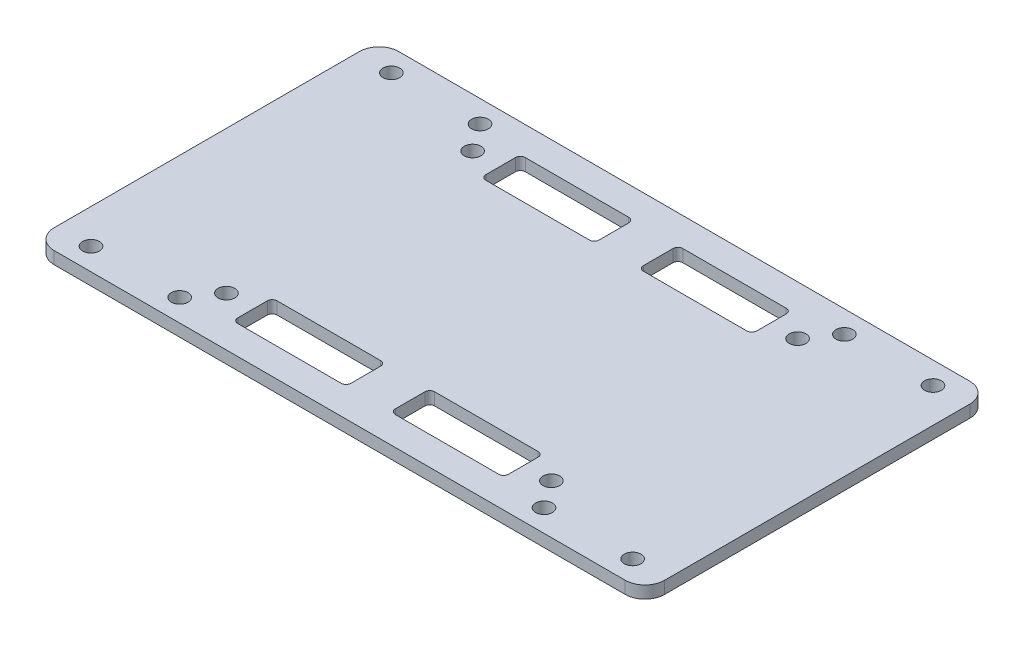
SolidWorks part; units mm, degrees
ref_plane "前视基准面" through (0, 0, 0) normal (0, 0, 1) x (1, 0, 0)
ref_plane "上视基准面" through (0, 0, 0) normal (0, 1, 0) x (1, 0, 0)
ref_plane "右视基准面" through (0, 0, 0) normal (1, 0, 0) x (0, 0, -1)
other "Configuration Table"
sketch "草图1" plane through (0, 0, 0) normal (0, 1, 0) x (1, 0, 0)
  line L0 (-0.8163, -21.6753) -> (22.1837, -21.6753)
  line L1 (-67.3163, 34.5247) -> (56.6837, 34.5247)
  line L2 (-67.3163, 34.5247) -> (-67.3163, -35.4753)
  line L3 (-67.3163, -35.4753) -> (56.6837, -35.4753)
  line L4 (56.6837, 34.5247) -> (56.6837, -35.4753)
  line L5 (-32.8163, -21.6753) -> (-9.8163, -21.6753)
  line L6 (-32.8163, -21.6753) -> (-32.8163, -29.6753)
  line L7 (-32.8163, -29.6753) -> (-9.8163, -29.6753)
  line L8 (-9.8163, -21.6753) -> (-9.8163, -29.6753)
  line L9 (-0.8163, -21.6753) -> (-0.8163, -29.6753)
  line L10 (-0.8163, -29.6753) -> (22.1837, -29.6753)
  line L11 (22.1837, -21.6753) -> (22.1837, -29.6753)
  line L12 (-32.8163, 28.7247) -> (-9.8163, 28.7247)
  line L13 (-32.8163, 28.7247) -> (-32.8163, 20.7247)
  line L14 (-32.8163, 20.7247) -> (-9.8163, 20.7247)
  line L15 (-9.8163, 28.7247) -> (-9.8163, 20.7247)
  line L16 (-0.8163, 28.7247) -> (22.1837, 28.7247)
  line L17 (-0.8163, 28.7247) -> (-0.8163, 20.7247)
  line L18 (-0.8163, 20.7247) -> (22.1837, 20.7247)
  line L19 (22.1837, 28.7247) -> (22.1837, 20.7247)
  circle A0 centre (49.6837, -30.9753) radius 1.7
  circle A1 centre (49.6837, 30.0247) radius 1.7
  circle A2 centre (-60.3163, 30.0247) radius 1.7
  circle A3 centre (-60.3163, -30.9753) radius 1.7
  circle A4 centre (-42.3163, -30.9753) radius 1.7
  circle A6 centre (-38.3163, -25.4753) radius 1.7
  circle A7 centre (31.6837, -30.9753) radius 1.7
  circle A8 centre (27.6837, -25.4753) radius 1.7
  circle A9 centre (31.6837, 30.0247) radius 1.7
  circle A10 centre (27.6837, 24.5247) radius 1.7
  circle A11 centre (-42.3163, 30.0247) radius 1.7
  circle A12 centre (-38.3163, 24.5247) radius 1.7
  dimension "D3" = 7
  dimension "D5" = 7
  dimension "D1" = 124
  dimension "D2" = 70
  dimension "D4" = 4.5
  dimension "D6" = 4.5
  dimension "D7" = 7
  dimension "D8" = 4.5
  dimension "D9" = 4.5
  dimension "D10" = 7
  dimension "D11" = 4.5
  dimension "D12" = 4.5
  dimension "D13" = 25
  dimension "D14" = 25
  dimension "D15" = 25
  dimension "D16" = 25
  dimension "D17" = 4.5
  dimension "D18" = 4.5
  dimension "D19" = 10
  dimension "D20" = 10
  dimension "D21" = 10
  dimension "D22" = 10
  dimension "D23" = 29
  dimension "D24" = 29
  dimension "D25" = 29
  dimension "D26" = 29
  dimension "D27" = 8
  dimension "D28" = 23
  dimension "D29" = 8
  dimension "D30" = 23
  dimension "D31" = 8
  dimension "D32" = 23
  dimension "D33" = 8
  dimension "D34" = 23
  dimension "D35" = 5.8
  dimension "D36" = 5.8
  dimension "D37" = 5.8
  dimension "D38" = 5.8
  dimension "D39" = 34.5
  dimension "D40" = 34.5
  dimension "D41" = 34.5
  dimension "D42" = 34.5
extrude "凸台-拉伸1" add sketch "草图1" along normal blind 2.5
fillet "圆角1" radius 4 1 edges at (-67.3163, 1.25, 35.4753)
fillet "圆角2" radius 4 1 edges at (-67.3163, 1.25, -34.5247)
fillet "圆角3" radius 4 1 edges at (56.6837, 1.25, 35.4753)
fillet "圆角4" radius 4 1 edges at (56.6837, 1.25, -34.5247)
fillet "圆角6" radius 1 4 edges at (22.1837, 1.25, -20.7247) (-0.8163, 1.25, -20.7247) (-0.8163, 1.25, -28.7247) (22.1837, 1.25, -28.7247)
fillet "圆角8" radius 1 4 edges at (-9.8163, 1.25, -20.7247) (-32.8163, 1.25, -20.7247) (-9.8163, 1.25, -28.7247) (-32.8163, 1.25, -28.7247)
fillet "圆角9" radius 1 8 edges at (22.1837, 1.25, 29.6753) (-0.8163, 1.25, 21.6753) (-0.8163, 1.25, 29.6753) (22.1837, 1.25, 21.6753) (-9.8163, 1.25, 29.6753) (-32.8163, 1.25, 29.6753) (-9.8163, 1.25, 21.6753) (-32.8163, 1.25, 21.6753)
